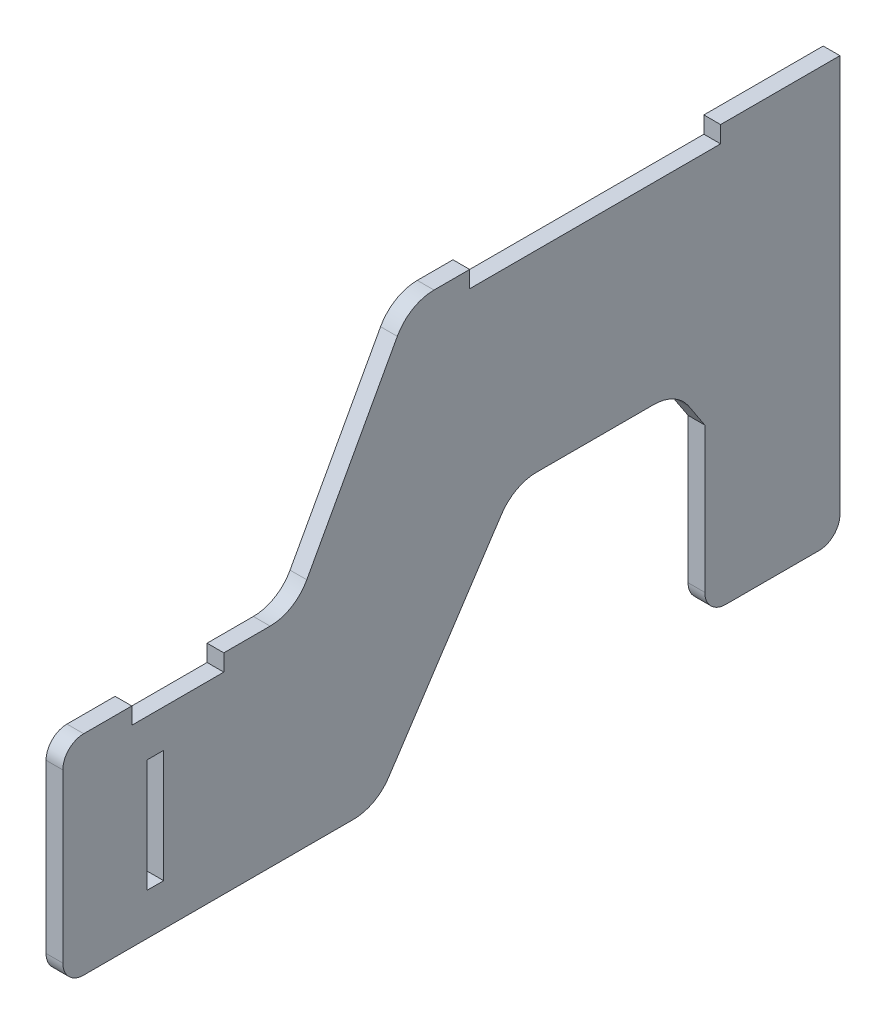
SolidWorks part; units mm, degrees
ref_plane "Front Plane" through (0, 0, 0) normal (0, 0, 1) x (1, 0, 0)
ref_plane "Top Plane" through (0, 0, 0) normal (0, 1, 0) x (1, 0, 0)
ref_plane "Right Plane" through (0, 0, 0) normal (1, 0, 0) x (0, 0, -1)
sketch "Sketch2" plane through (0, 0, 0) normal (1, 0, 0) x (0, 0, -1)
  line L10 (53.3446, -85.4988) -> (74.9872, -45.9059)
  line L20 (83.7618, -40.7023) -> (92.2965, -40.7023)
  line L21 (122.2965, -63.5687) -> (122.2965, -90.7023) construction
  line L22 (136.3192, -90.7023) -> (108.2738, -90.7023)
  line L23 (72.9083, -136.204) -> (99.9233, -95.2006)
  line L24 (191.2484, -85.4988) -> (169.6058, -45.9059)
  line L25 (171.6847, -136.204) -> (144.6697, -95.2006)
  line L29 (92.2965, -40.7023) -> (92.2965, -44.7023)
  line L30 (92.2965, -44.7023) -> (152.2965, -44.7023)
  line L31 (152.2965, -40.7023) -> (152.2965, -44.7023)
  line L32 (152.2965, -40.7023) -> (160.8312, -40.7023)
  line L33 (38.5351, -90.7023) -> (44.57, -90.7023)
  line L34 (11.5002, -90.7023) -> (11.5002, -94.7023)
  line L35 (11.5002, -94.7023) -> (33.5002, -94.7023)
  line L38 (233.0928, -94.7023) -> (211.0928, -94.7023)
  line L39 (233.0928, -90.7023) -> (233.0928, -94.7023)
  line L40 (206.0579, -90.7023) -> (200.023, -90.7023)
  line L41 (22.5002, -101.0419) -> (22.5002, -137.1323) construction
  line L45 (18.3738, -140.7023) -> (18.3738, -117.2023) construction
  line L55 (33.5002, -94.7023) -> (33.5002, -90.7023)
  line L56 (33.5002, -90.7023) -> (38.5351, -90.7023)
  line L57 (211.0928, -94.7023) -> (211.0928, -90.7023)
  line L58 (211.0928, -90.7023) -> (206.0579, -90.7023)
  line L60 (-5, -95.7023) -> (-5, -135.7023)
  line L62 (249.9368, -95.8211) -> (248.9863, -135.8211)
  line L65 (233.0928, -90.7023) -> (244.9382, -90.7023)
  line L66 (180.0352, -140.7023) -> (243.9878, -140.7023)
  line L67 (0, -140.7023) -> (64.5578, -140.7023)
  line L68 (0, -90.7023) -> (11.5002, -90.7023)
  line L69 (225.463, -130.7023) -> (229.463, -130.7023)
  line L70 (19.13, -103.7023) -> (15.13, -103.7023)
  line L71 (19.13, -103.7023) -> (19.13, -130.7023)
  line L72 (19.13, -130.7023) -> (15.13, -130.7023)
  line L73 (15.13, -103.7023) -> (15.13, -130.7023)
  line L74 (229.463, -103.7023) -> (229.463, -130.7023)
  line L75 (225.463, -103.7023) -> (229.463, -103.7023)
  line L76 (225.463, -103.7023) -> (225.463, -130.7023)
  arc A0 (74.9872, -45.9059) -> (83.7618, -40.7023) centre (83.7618, -50.7023) cw
  arc A2 (72.9083, -136.204) -> (64.5578, -140.7023) centre (64.5578, -130.7023) cw
  arc A3 (99.9233, -95.2006) -> (108.2738, -90.7023) centre (108.2738, -100.7023) cw
  arc A4 (44.57, -90.7023) -> (53.3446, -85.4988) centre (44.57, -80.7023) ccw
  arc A6 (144.6697, -95.2006) -> (136.3192, -90.7023) centre (136.3192, -100.7023) ccw
  arc A7 (169.6058, -45.9059) -> (160.8312, -40.7023) centre (160.8312, -50.7023) ccw
  arc A8 (200.023, -90.7023) -> (191.2484, -85.4988) centre (200.023, -80.7023) cw
  arc A9 (171.6847, -136.204) -> (180.0352, -140.7023) centre (180.0352, -130.7023) ccw
  arc A11 (249.9368, -95.8211) -> (244.9382, -90.7023) centre (244.9382, -95.7023) ccw
  arc A12 (248.9863, -135.8211) -> (243.9878, -140.7023) centre (243.9878, -135.7023) cw
  arc A13 (-5, -135.7023) -> (0, -140.7023) centre (0, -135.7023) ccw
  arc A14 (-5, -95.7023) -> (0, -90.7023) centre (0, -95.7023) cw
  point P10 (77.8316, -40.7023)
  point P14 (0.5002, -90.7023)
  point P17 (70.5002, -140.7023)
  point P22 (50.5002, -90.7023)
  point P25 (0.5002, -140.7023)
  point P48 (122.2965, -44.7023)
  point P56 (22.5002, -94.7023)
  point P67 (22.5002, -131.7023)
  point P68 (22.5002, -104.7023)
  dimension "D4" = 10
  dimension "D5" = 10
  dimension "D7" = 10
  dimension "D9" = 5
  dimension "D19" = 5
  dimension "D20" = 5
  dimension "D17" = 5
  dimension "D1" = 50
  dimension "D2" = 50
  dimension "D3" = 50
  dimension "D6" = 70
  dimension "D8" = 100
  dimension "D10" = 56.9825
  dimension "D11" = 4
  dimension "D12" = 30
  dimension "D13" = 11
  dimension "D14" = 4
  dimension "D15" = 100
  dimension "D16" = 23.5
  dimension "D21" = 4
  dimension "D22" = 20.13
extrude "Boss-Extrude1" add sketch "Sketch2" along normal blind 4
sketch "Sketch3" plane through (0, 0, 0) normal (1, 0, 0) x (0, 0, -1)
  line L0 (160.8312, -40.7023) -> (160.8312, -144.4609)
  line L1 (160.8312, -144.4609) -> (257.8753, -144.4609)
  line L2 (257.8753, -144.4609) -> (257.8753, -25.5441)
  line L3 (257.8753, -25.5441) -> (160.8312, -34.9038)
  line L4 (160.8312, -34.9038) -> (160.8312, -40.7023)
extrude "Cut-Extrude1" cut sketch "Sketch3" along normal blind 10
sketch "Sketch4" plane through (0, 0, 0) normal (1, 0, 0) x (0, 0, -1)
  line L0 (160.8312, -40.7023) -> (180.8312, -40.7023)
  line L1 (180.8312, -40.7023) -> (180.8312, -135.7023)
  line L2 (153.525, -140.7023) -> (175.8312, -140.7023)
  line L3 (148.525, -101.0522) -> (148.525, -135.7023)
  line L4 (144.6697, -95.2006) -> (160.8312, -119.7305) construction
  line L5 (160.8312, -40.7023) -> (148.525, -101.0522)
  arc A0 (175.8312, -140.7023) -> (180.8312, -135.7023) centre (175.8312, -135.7023) ccw
  arc A1 (148.525, -135.7023) -> (153.525, -140.7023) centre (153.525, -135.7023) ccw
  dimension "D2" = 5
  dimension "D1" = 20
extrude "Boss-Extrude2" add sketch "Sketch4" along normal blind 4
